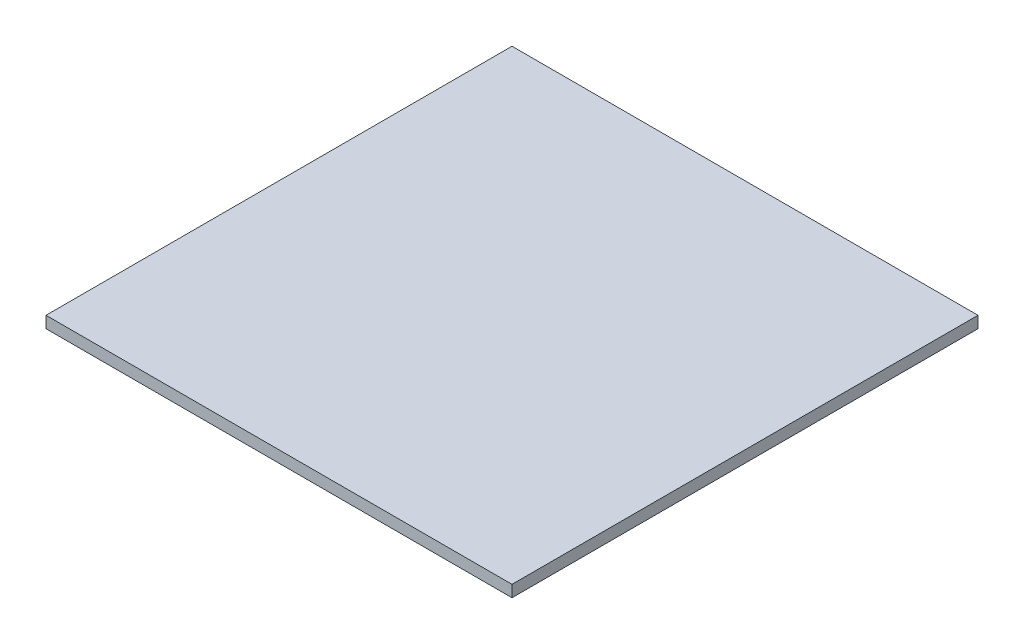
SolidWorks part; units mm, degrees
ref_plane "Front Plane" through (0, 0, 0) normal (0, 0, 1) x (1, 0, 0)
ref_plane "Top Plane" through (0, 0, 0) normal (0, 1, 0) x (1, 0, 0)
ref_plane "Right Plane" through (0, 0, 0) normal (1, 0, 0) x (0, 0, -1)
sketch "Sketch1" plane through (0, 0, 0) normal (0, 1, 0) x (1, 0, 0)
  line L1 (-200, -200) -> (200, -200)
  line L2 (-200, -200) -> (-200, 200)
  line L3 (-200, 200) -> (200, 200)
  line L4 (200, -200) -> (200, 200)
  line L5 (-200, -200) -> (200, 200) construction
  line L6 (-200, 200) -> (200, -200) construction
  point P0 (0, 0)
  dimension "D1" = 400
  dimension "D2" = 400
extrude "Boss-Extrude1" add sketch "Sketch1" along normal blind 10
sketch "Sketch2" plane through (0, 10, 0) normal (0, 1, 0) x (1, 0, 0)
  line L0 (-200, -200) -> (200, 200) construction
  line L1 (-200, 200) -> (200, -200) construction
  line L2 (0, 200) -> (0, -200) construction
  line L3 (200, 200) -> (-200, 200) construction
  line L4 (-200, -200) -> (200, -200) construction
  line L5 (-200, 0) -> (200, 0) construction
  line L6 (-200, 200) -> (-200, -200) construction
  line L7 (200, -200) -> (200, 200) construction
